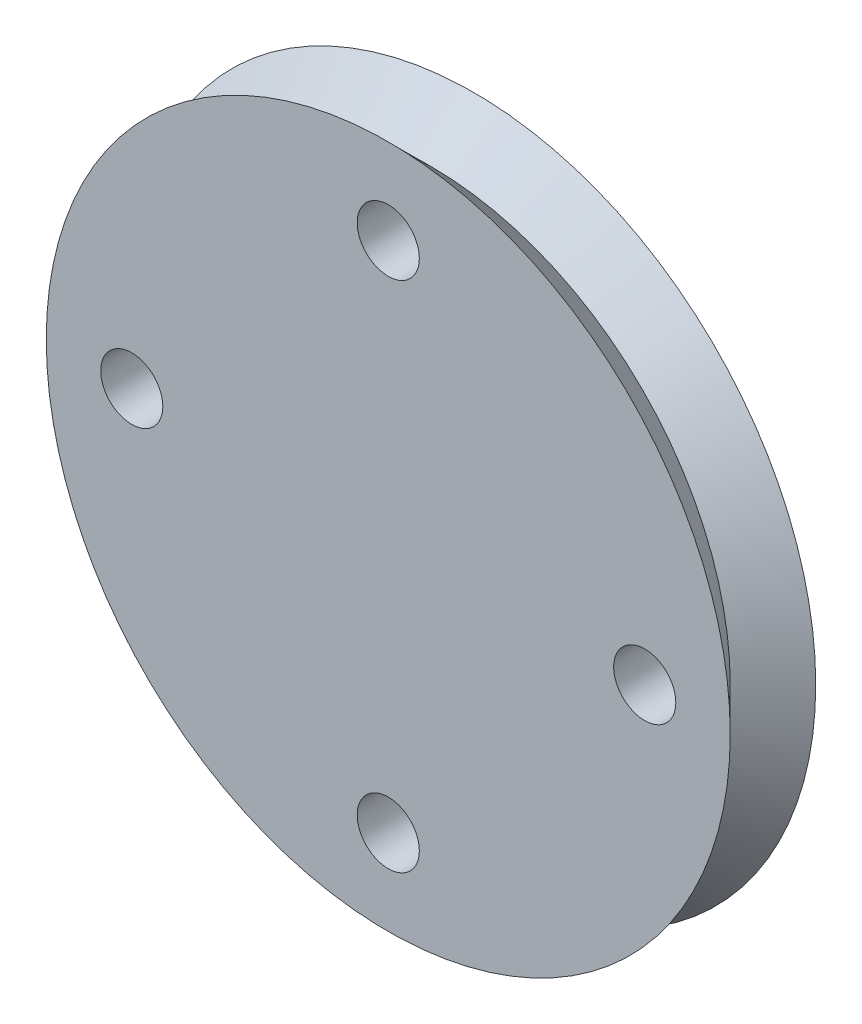
SolidWorks part; units mm, degrees
ref_plane "Front Plane" through (0, 0, 0) normal (0, 0, 1) x (1, 0, 0)
ref_plane "Top Plane" through (0, 0, 0) normal (0, 1, 0) x (1, 0, 0)
ref_plane "Right Plane" through (0, 0, 0) normal (1, 0, 0) x (0, 0, -1)
sketch "Sketch1" plane through (0, 0, 0) normal (0, 0, 1) x (1, 0, 0)
  circle A0 centre (0, 0) radius 8
extrude "Boss-Extrude1" add sketch "Sketch1" along normal blind 2
sketch "Sketch2" plane through (0, 0, 0) normal (0, 0, 1) x (1, 0, 0)
  line L0 (0, 8.3764) -> (0, -8.7503) construction
  line L1 (-8.6412, 0) -> (9.8917, 0) construction
  circle A0 centre (-6, 0) radius 0.7264
  circle A2 centre (0, 6) radius 0.7264
  circle A3 centre (6, 0) radius 0.7264
  circle A4 centre (0, -6) radius 0.7264
  dimension "D1" = 4
  dimension "D2" = 12
extrude "Cut-Extrude1" cut sketch "Sketch2" along normal up to surface (2 mm away) up to face at (8, 0, 2)
sketch "Sketch3" plane through (0, 0, 0) normal (1, 0, 0) x (0, 0, -1)
  line L0 (-2, 8) -> (-1, 7)
  line L1 (-1, 7) -> (0, 8)
  line L2 (0, 8) -> (-2, 8)
  line L3 (-3.5023, 0) -> (1.8955, 0) construction
  line L4 (-1, 8.4494) -> (-1, 6.6462) construction
  point P10 (0, 0)
  dimension "D1" = 90
revolve "Cut-Revolve1" cut sketch "Sketch3" angle 360 about L3
